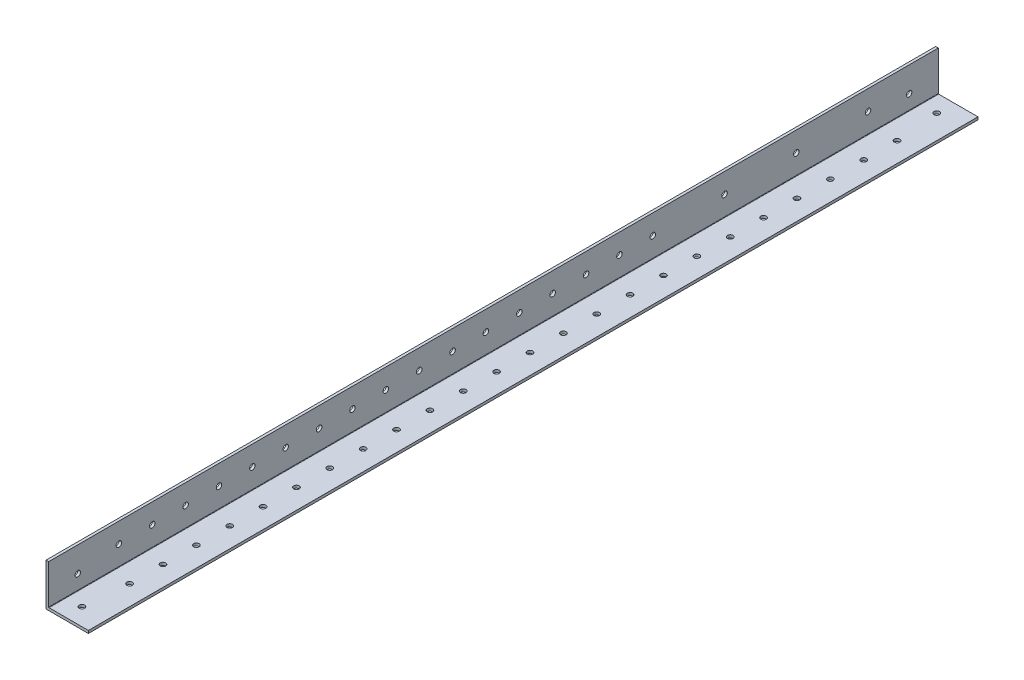
SolidWorks part; units mm, degrees
material "6061 Alloy"
ref_plane "Front Plane" through (0, 0, 0) normal (0, 0, 1) x (1, 0, 0)
ref_plane "Top Plane" through (0, 0, 0) normal (0, 1, 0) x (1, 0, 0)
ref_plane "Right Plane" through (0, 0, 0) normal (1, 0, 0) x (0, 0, -1)
sketch "Sketch1" plane through (0, 0, 0) normal (0, 0, 1) x (1, 0, 0)
  line L0 (0, 25.4) -> (0, 0) construction
  line L1 (0, 0) -> (25.4, 0) construction
  line L2 (25.4, 0) -> (25.4, 1.5875) construction
  line L3 (25.4, 1.5875) -> (1.5875, 1.5875) construction
  line L4 (1.5875, 1.5875) -> (1.5875, 25.4) construction
  line L6 (1.5875, 25.4) -> (0, 25.4) construction
  arc A0 (1.5875, 1.8415) -> (1.8415, 1.5875) centre (1.8415, 1.8415) ccw construction
  point P4 (0, 0)
  dimension "Inside Corner Radius" = 0.254
  dimension "Outside Height" = 25.4
  dimension "Inside Height" = 23.8125
  dimension "Outside Width" = 25.4
  dimension "Inside Width" = 23.8125
  dimension "Wall Thickness" = 1.5875
  dimension "Shape" = 90
sketch "Sketch2" plane through (0, 0, 0) normal (1, 0, 0) x (0, 0, -1)
  line L0 (1219.2, 0) -> (-1219.2, 0) construction
  line L1 (-1219.2, 25.4) -> (-1219.2, 0) construction
  line L2 (1219.2, 25.4) -> (1219.2, 0) construction
  point P0 (-1189.99, 0)
  point P4 (0, 0)
  point P6 (1189.99, 0)
  dimension "D1" = 29.21
  dimension "D2" = 29.21
  dimension "D3" = 25.4
  dimension "Length" = 2438.4
sketch "Sketch3" plane through (0, 0, 0) normal (0, 0, 1) x (1, 0, 0)
  line L0 (1.5875, 25.4) -> (0, 25.4)
  line L1 (0, 25.4) -> (0, 0)
  line L2 (0, 0) -> (25.4, 0)
  line L3 (25.4, 0) -> (25.4, 1.5875)
  line L4 (25.4, 1.5875) -> (1.5875, 1.5875)
  line L5 (1.5875, 1.5875) -> (1.5875, 25.4)
extrude "Boss-Extrude1" add sketch "Sketch3" along normal mid plane 2438.4
fillet "Fillet1" radius 0.254 1 edges at (1.5875, 1.5875, 0)
sketch "Sketch4" plane through (0, 0, 0) normal (-1, 0, 0) x (0, 0, 1)
  line L0 (-1219.2, 25.4) -> (-1219.2, 0) construction
  line L1 (-1219.2, 38.8591) -> (686, 38.8591)
  line L2 (-1219.2, 38.8591) -> (-1219.2, -53.7146)
  line L3 (-1219.2, -53.7146) -> (686, -53.7146)
  line L4 (686, 38.8591) -> (686, -53.7146)
  line L6 (1219.2, 25.4) -> (1219.2, 0) construction
  dimension "D1" = 533.2
extrude "Cut-Extrude1" cut sketch "Sketch4" against normal blind 60
sketch "Sketch9" plane through (0, 1.5875, 0) normal (0, 1, 0) x (1, 0, 0)
  line L0 (1.5875, -1182.6) -> (25.4, -1182.6) construction
  line L1 (1.5875, -1219.2) -> (1.5875, -686) construction
  line L2 (25.4, -1219.2) -> (25.4, -686) construction
  line L3 (11.113, -1208.7918) -> (11.113, -1182.6) construction
  line L4 (13.4937, -722.6) -> (25.4, -722.6) construction
  line L5 (13.4937, -722.6) -> (13.4937, -696.4082) construction
  line L6 (13.4937, -696.4082) -> (11.1125, -696.4082) construction
  line L7 (11.1125, -696.4082) -> (13.4937, -696.4082) construction
  circle A0 centre (11.113, -1208.7918) radius 1.65
  circle A1 centre (11.1125, -696.4082) radius 1.65
  circle A2 centre (13.4938, -1182.6) radius 1.65
  circle A3 centre (13.4938, -1162.6) radius 1.65
  circle A4 centre (13.4938, -1142.6) radius 1.65
  circle A5 centre (13.4938, -1122.6) radius 1.65
  circle A6 centre (13.4938, -1102.6) radius 1.65
  circle A7 centre (13.4938, -1082.6) radius 1.65
  circle A8 centre (13.4938, -1062.6) radius 1.65
  circle A9 centre (13.4938, -1042.6) radius 1.65
  circle A10 centre (13.4938, -1022.6) radius 1.65
  circle A11 centre (13.4938, -1002.6) radius 1.65
  circle A12 centre (13.4938, -982.6) radius 1.65
  circle A13 centre (13.4938, -962.6) radius 1.65
  circle A14 centre (13.4938, -942.6) radius 1.65
  circle A15 centre (13.4938, -922.6) radius 1.65
  circle A16 centre (13.4938, -902.6) radius 1.65
  circle A17 centre (13.4938, -882.6) radius 1.65
  circle A18 centre (13.4938, -862.6) radius 1.65
  circle A19 centre (13.4938, -842.6) radius 1.65
  circle A20 centre (13.4938, -822.6) radius 1.65
  circle A21 centre (13.4938, -802.6) radius 1.65
  circle A22 centre (13.4938, -782.6) radius 1.65
  circle A23 centre (13.4938, -762.6) radius 1.65
  circle A24 centre (13.4938, -742.6) radius 1.65
  circle A25 centre (13.4937, -722.6) radius 1.65
  dimension "D1" = 3.3
  dimension "D3" = 20
  dimension "D2" = 24
extrude "Cut-Extrude6" cut sketch "Sketch9" against normal blind 60
sketch "Sketch10" plane through (1.5875, 0, 0) normal (1, 0, 0) x (0, 0, -1)
  line L0 (-728.1, 25.4) -> (-728.1, 1.5875) construction
  line L3 (-1219.2, 25.4) -> (-686, 25.4) construction
  line L4 (-1219.2, 1.5875) -> (-686, 1.5875) construction
  line L5 (-728.1, 13.4937) -> (-703.4625, 13.4937) construction
  line L6 (-703.4625, 13.4937) -> (-703.4625, 10.3759) construction
  line L7 (-1201.7375, 10.3759) -> (-1201.7375, 25.4) construction
  line L8 (-1177.1, 13.4937) -> (-1201.7375, 13.4937) construction
  circle A0 centre (-703.4625, 10.3759) radius 1.65
  circle A1 centre (-1201.7375, 10.3759) radius 1.65
  circle A2 centre (-728.1, 13.4937) radius 1.65
  circle A3 centre (-771.1, 13.4937) radius 1.65
  circle A4 centre (-814.1, 13.4937) radius 1.65
  circle A5 centre (-857.1, 13.4937) radius 1.65
  circle A6 centre (-877.1, 13.4937) radius 1.65
  circle A7 centre (-897.1, 13.4937) radius 1.65
  circle A8 centre (-917.1, 13.4937) radius 1.65
  circle A9 centre (-937.1, 13.4937) radius 1.65
  circle A10 centre (-957.1, 13.4937) radius 1.65
  circle A11 centre (-977.1, 13.4937) radius 1.65
  circle A12 centre (-997.1, 13.4937) radius 1.65
  circle A13 centre (-1017.1, 13.4937) radius 1.65
  circle A14 centre (-1037.1, 13.4937) radius 1.65
  circle A15 centre (-1057.1, 13.4937) radius 1.65
  circle A16 centre (-1077.1, 13.4937) radius 1.65
  circle A17 centre (-1097.1, 13.4937) radius 1.65
  circle A18 centre (-1117.1, 13.4937) radius 1.65
  circle A19 centre (-1137.1, 13.4937) radius 1.65
  circle A20 centre (-1157.1, 13.4937) radius 1.65
  circle A21 centre (-1177.1, 13.4937) radius 1.65
  dimension "D1" = 3.3
  dimension "D3" = 43
  dimension "D4" = 20
  dimension "D2" = 4
extrude "Cut-Extrude7" cut sketch "Sketch10" against normal blind 60
equation "\"D1@Boss-Extrude1\"=\"Length@Sketch2\""
equation "\"D1@Sketch2\" = \"Outside Width@Sketch1\" * 1.15"
equation "\"D2@Sketch2\"=\"D1@Sketch2\""
equation "\"D1@Fillet1\"=\"Inside Corner Radius@Sketch1\""
equation "\"D3@Sketch2\"=\"Outside Height@Sketch1\""
